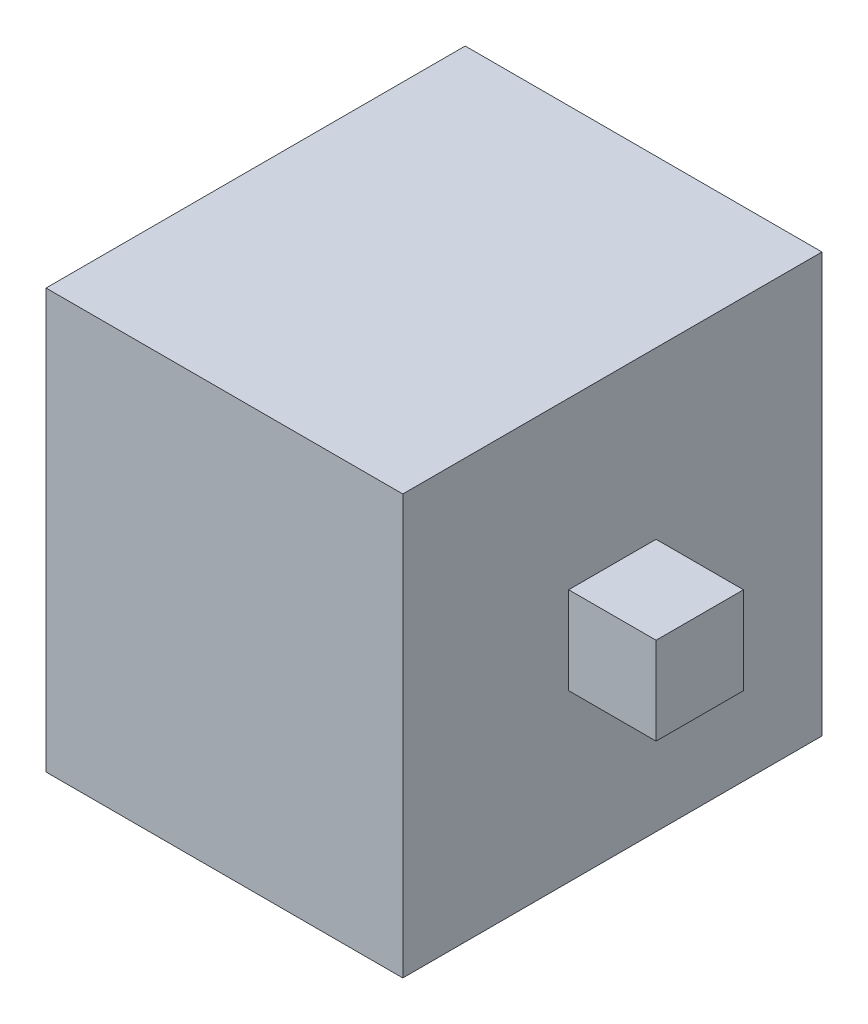
SolidWorks part; units mm, degrees
ref_plane "Alzado" through (0, 0, 0) normal (0, 0, 1) x (1, 0, 0)
ref_plane "Planta" through (0, 0, 0) normal (0, 1, 0) x (1, 0, 0)
ref_plane "Vista lateral" through (0, 0, 0) normal (1, 0, 0) x (0, 0, -1)
sketch "Croquis1" plane through (0, 0, 0) normal (0, 0, 1) x (1, 0, 0)
  line L1 (100, 117.5) -> (-100, 117.5)
  line L2 (100, 117.5) -> (100, -117.5)
  line L3 (100, -117.5) -> (-100, -117.5)
  line L4 (-100, 117.5) -> (-100, -117.5)
  line L5 (100, 117.5) -> (-100, -117.5) construction
  line L6 (100, -117.5) -> (-100, 117.5) construction
  point P0 (0, 0)
  dimension "D1" = 235
  dimension "D2" = 200
extrude "Saliente-Extruir1" add sketch "Croquis1" along normal blind 235
sketch "Croquis2" plane through (100, 0, 0) normal (1, 0, 0) x (0, 0, -1)
  line L0 (-117.5, -117.5) -> (-117.5, 117.5) construction
  line L1 (-235, -117.5) -> (0, -117.5) construction
  line L2 (-235, 117.5) -> (0, 117.5) construction
  line L3 (0, 0) -> (-235, 0) construction
  line L4 (-235, -117.5) -> (-235, 117.5) construction
  line L6 (-93, 24.5) -> (-142, 24.5)
  line L7 (-93, 24.5) -> (-93, -24.5)
  line L8 (-93, -24.5) -> (-142, -24.5)
  line L9 (-142, 24.5) -> (-142, -24.5)
  line L10 (-93, 24.5) -> (-142, -24.5) construction
  line L11 (-93, -24.5) -> (-142, 24.5) construction
  point P11 (-117.5, 0)
  dimension "D1" = 49
extrude "Saliente-Extruir2" add sketch "Croquis2" along normal blind 49
